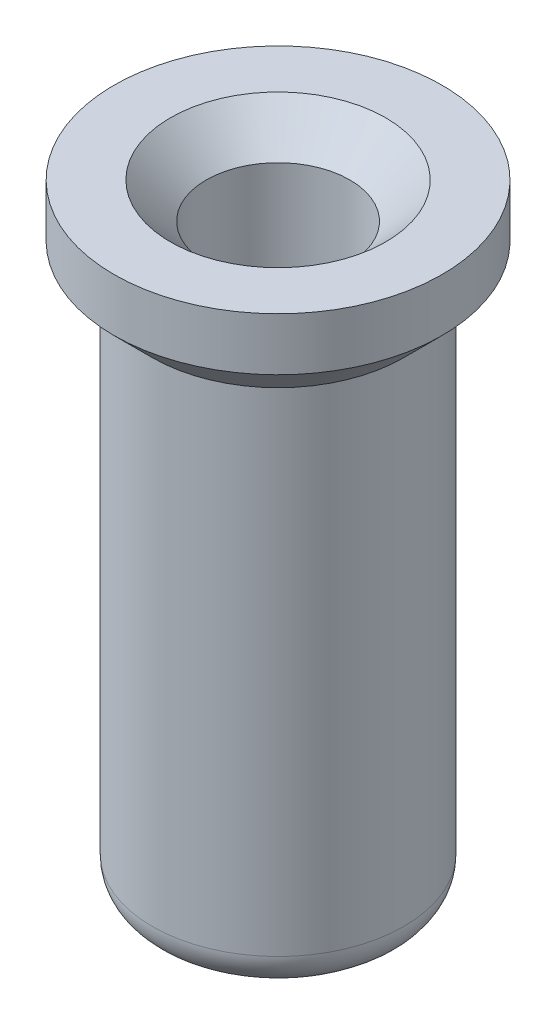
SolidWorks part; units mm, degrees
ref_plane "Front Plane" through (0, 0, 0) normal (0, 0, 1) x (1, 0, 0)
ref_plane "Top Plane" through (0, 0, 0) normal (0, 1, 0) x (1, 0, 0)
ref_plane "Right Plane" through (0, 0, 0) normal (1, 0, 0) x (0, 0, -1)
sketch "Sketch1" plane through (0, 0, 0) normal (1, 0, 0) x (0, 0, -1)
  line L0 (0, 1.873) -> (0, -1.6961) construction
  line L1 (0, 2.159) -> (1.143, 2.159)
  line L2 (1.143, 2.159) -> (1.143, 1.7907)
  line L3 (1.143, 1.7907) -> (0.8763, 1.524)
  line L4 (0.8763, 1.524) -> (0.8763, -2.159)
  line L5 (0.8763, -2.159) -> (0, -2.159)
  line L6 (0.4382, -2.159) -> (0.4382, 2.159) construction
  line L7 (0, 2.159) -> (0, -2.159)
  point P11 (0.4382, 0)
  dimension "D1" = 2.286
  dimension "D2" = 1.7526
  dimension "D3" = 4.318
  dimension "D4" = 0.635
  dimension "D5" = 135
revolve "Revolve1" add sketch "Sketch1" angle 360 about L7
hole_wizard "Ø1.0 (1) Diameter Hole1" positions "3DSketch1" profile "Sketch2" hole size "Ø1.0" standard "ANSI Metric"
sketch3d "3DSketch1"
  line L0 (0, 1.7907, 0) -> (0, 2.159, 0) construction
  point P0 (0, 2.159, 0)
sketch "Sketch2" plane through (0, 2.159, 0) normal (1, 0, 0) x (0, 0, 1)
  line L0 (0, 0) -> (0, 4.0342)
  line L1 (0, 4.0342) -> (0.5, 3.7338)
  line L2 (0.5, 3.7338) -> (0.5, 0)
  line L5 (0.5, 0) -> (0, 0)
  line L10 (0, 4.0342) -> (-0.5, 3.7338) construction
  line L11 (0, -6.35) -> (0, 107.95) construction
  dimension "Hole Dia." = 1
  dimension "Hole Depth" = 3.7338
  dimension "Drill Angle" = 118
fillet "Fillet1" radius 0.25 1 edges at (0, -2.159, 0.8763)
chamfer "Chamfer1" distance 0.25 angle 45 1 edges at (0, 2.159, 0.5)
